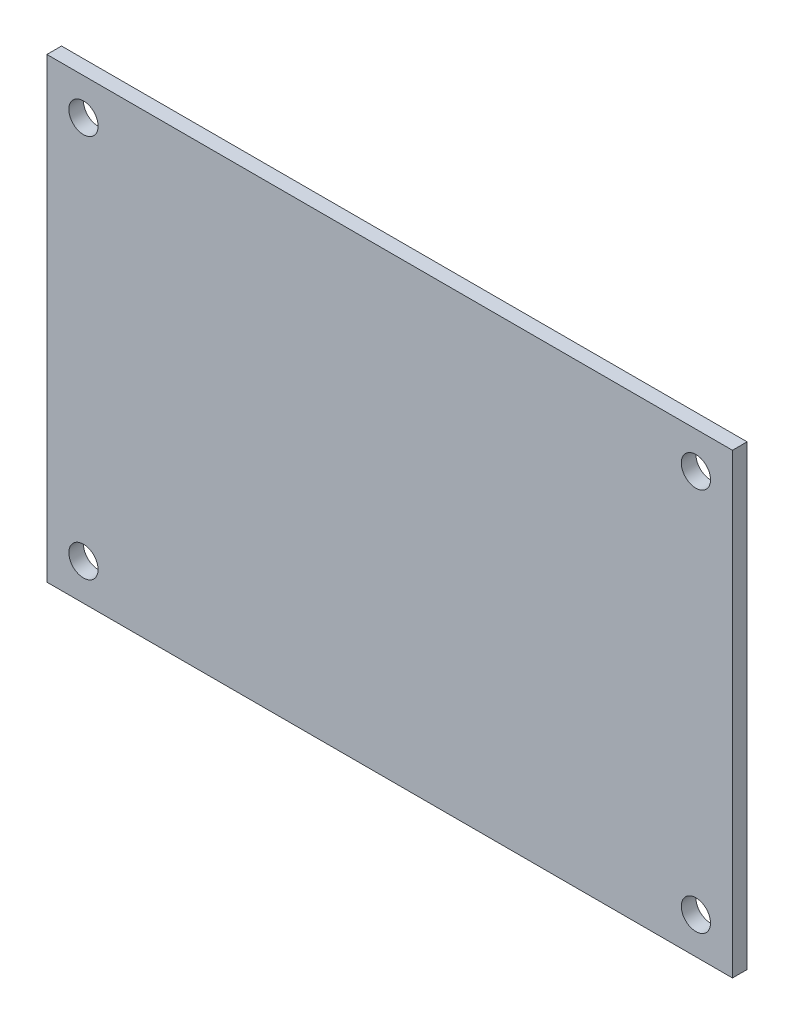
SolidWorks part; units mm, degrees
ref_plane "Front Plane" through (0, 0, 0) normal (0, 0, 1) x (1, 0, 0)
ref_plane "Top Plane" through (0, 0, 0) normal (0, 1, 0) x (1, 0, 0)
ref_plane "Right Plane" through (0, 0, 0) normal (1, 0, 0) x (0, 0, -1)
sketch "Sketch1" plane through (0, 0, 0) normal (0, 0, 1) x (1, 0, 0)
  line L0 (-37.5, 25) -> (37.5, -25) construction
  line L1 (-37.5, 25) -> (37.5, 25)
  line L2 (-37.5, 25) -> (-37.5, -25)
  line L3 (-37.5, -25) -> (37.5, -25)
  line L4 (37.5, 25) -> (37.5, -25)
  dimension "D1" = 75
  dimension "D2" = 50
extrude "Boss-Extrude1" add sketch "Sketch1" along normal blind 1.6
sketch "Sketch2" plane through (0, 0, 1.6) normal (0, 0, 1) x (1, 0, 0)
  line L0 (-33.5, 21) -> (33.5, -21) construction
  line L1 (-33.5, 21) -> (33.5, 21) construction
  line L2 (-33.5, 21) -> (-33.5, -21) construction
  line L3 (-33.5, -21) -> (33.5, -21) construction
  line L4 (33.5, 21) -> (33.5, -21) construction
  circle A0 centre (-33.5, 21) radius 1.6
  circle A1 centre (33.5, 21) radius 1.6
  circle A2 centre (33.5, -21) radius 1.6
  circle A3 centre (-33.5, -21) radius 1.6
  dimension "D1" = 3.2
  dimension "D2" = 67
  dimension "D3" = 42
extrude "Cut-Extrude1" cut sketch "Sketch2" against normal through all
